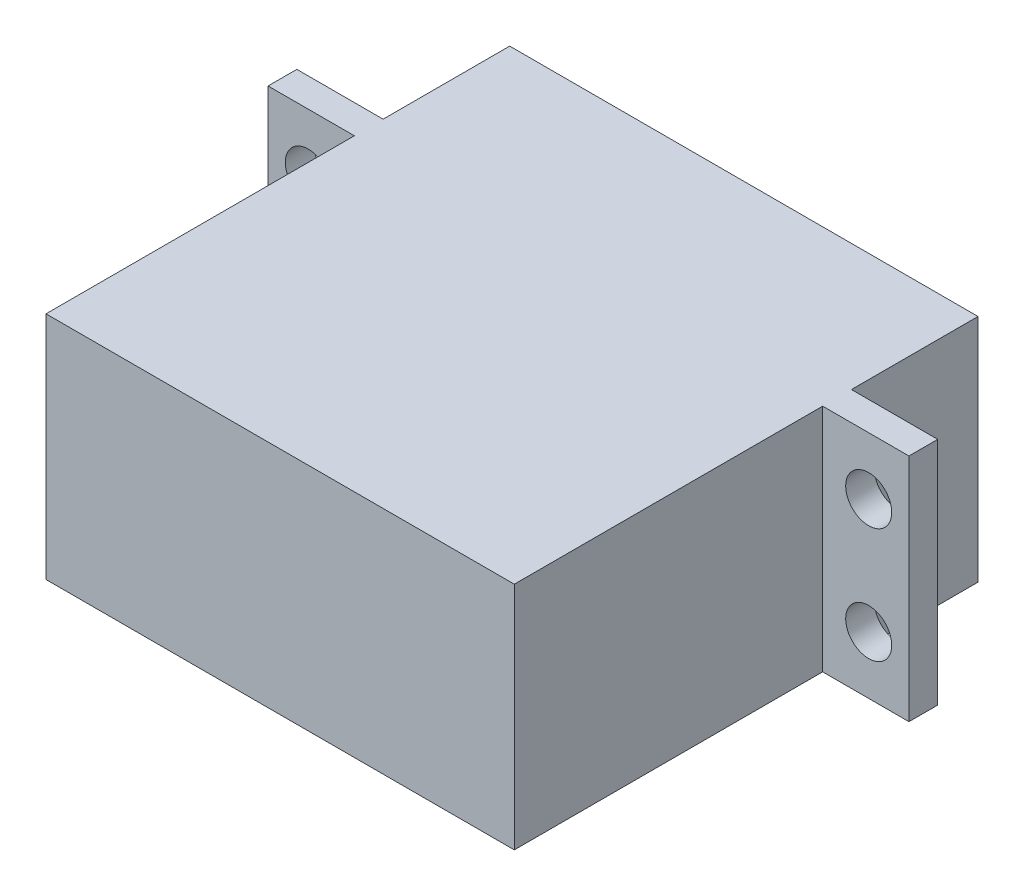
SolidWorks part; units mm, degrees
ref_plane "Piano frontale" through (0, 0, 0) normal (0, 0, 1) x (1, 0, 0)
ref_plane "Piano superiore" through (0, 0, 0) normal (0, 1, 0) x (1, 0, 0)
ref_plane "Piano destro" through (0, 0, 0) normal (1, 0, 0) x (0, 0, -1)
sketch "Schizzo1" plane through (0, 0, 0) normal (0, 0, 1) x (1, 0, 0)
  line L1 (-20.35, -10) -> (20.35, -10)
  line L2 (-20.35, -10) -> (-20.35, 10)
  line L3 (-20.35, 10) -> (20.35, 10)
  line L4 (20.35, -10) -> (20.35, 10)
  line L5 (-20.35, -10) -> (20.35, 10) construction
  line L6 (-20.35, 10) -> (20.35, -10) construction
  point P0 (0, 0)
  dimension "D1" = 40.7
  dimension "D2" = 20
extrude "Estrusione-Estrusione1" add sketch "Schizzo1" along normal blind 40.3
sketch "Schizzo2" plane through (20.35, 0, 0) normal (1, 0, 0) x (0, 0, -1)
  line L0 (0, 10) -> (-11, 10)
  line L1 (-40.3, 10) -> (0, 10) construction
  line L2 (-11, 10) -> (-11, -10)
  line L3 (-40.3, -10) -> (0, -10) construction
  line L4 (-11, -10) -> (0, -10)
  line L6 (-11, 10) -> (-13.5, 10)
  line L7 (-11, 10) -> (-11, -10)
  line L8 (-11, -10) -> (-13.5, -10)
  line L9 (-13.5, 10) -> (-13.5, -10)
  line M2 (0, 10) -> (-40.3, 10)
  line M4 (-40.3, -10) -> (0, -10)
  dimension "D1" = 11
  dimension "D2" = 2.5
extrude "Estrusione-Estrusione2" add sketch "Schizzo2" along normal blind 7.5 contours L9 L2 M2 M4
pattern_linear "Ripetizione a L1" count 2 spacing 48.2 along (-1, 0, 0) of "Estrusione-Estrusione2"
sketch "Schizzo3" plane through (0, 0, 0) normal (0, 0, -1) x (-1, 0, 0)
  line L0 (-20.35, -10) -> (-20.35, 10) construction
  circle A0 centre (-10.35, 0) radius 3
  dimension "D1" = 6
  dimension "D2" = 10
extrude "Estrusione-Estrusione3" add sketch "Schizzo3" along normal blind 4
sketch "Schizzo4" plane through (0, 0, 11) normal (0, 0, -1) x (-1, 0, 0)
  line L0 (20.35, -10) -> (27.85, -10) construction
  line L1 (-27.85, 10) -> (-20.35, 10) construction
  line L2 (-20.35, 10) -> (-20.35, -10) construction
  line L3 (20.35, 10) -> (20.35, -10) construction
  circle A0 centre (-24.35, 5) radius 2
  circle A1 centre (-24.35, -5) radius 2
  circle A2 centre (24.35, 5) radius 2
  circle A3 centre (24.35, -5) radius 2
  dimension "D1" = 4
  dimension "D2" = 4
  dimension "D3" = 4
  dimension "D4" = 4
  dimension "D8" = 4
  dimension "D5" = 10
  dimension "D6" = 10
  dimension "D7" = 4
  dimension "D9" = 5
  dimension "D10" = 5
extrude "Taglio-Estrusione1" cut sketch "Schizzo4" against normal blind 10
